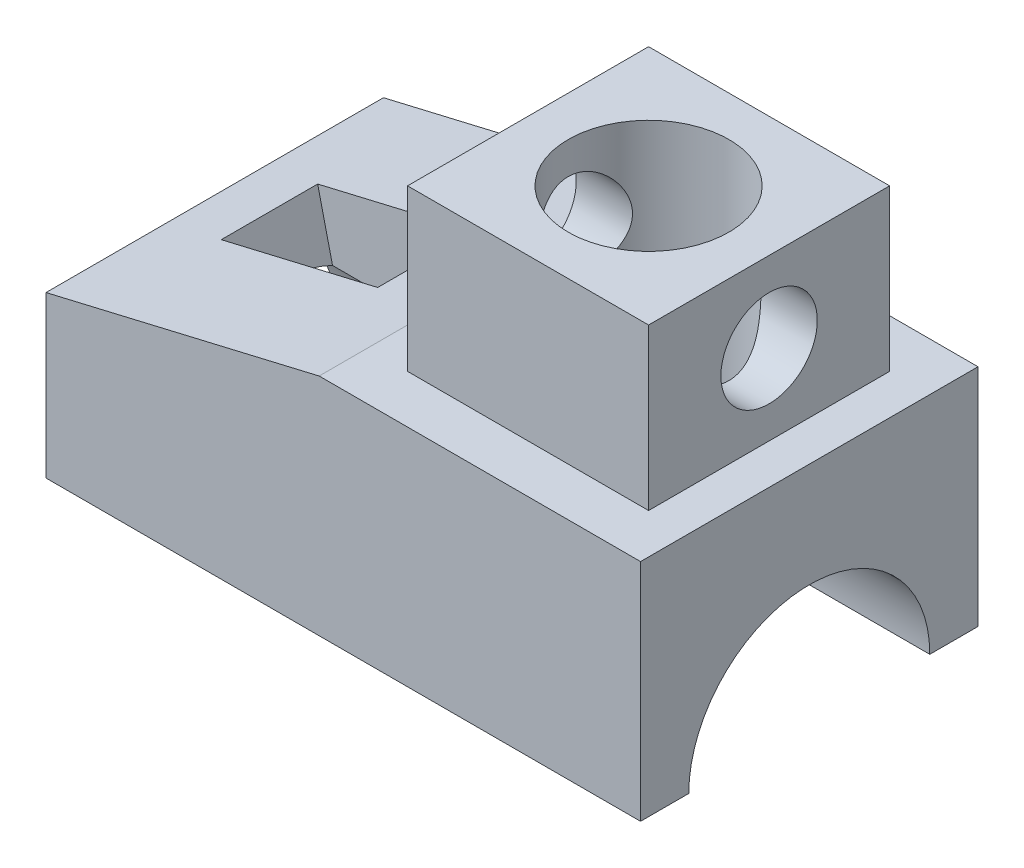
SolidWorks part; units mm, degrees
ref_plane "Front Plane" through (0, 0, 0) normal (0, 0, 1) x (1, 0, 0)
ref_plane "Top Plane" through (0, 0, 0) normal (0, 1, 0) x (1, 0, 0)
ref_plane "Right Plane" through (0, 0, 0) normal (1, 0, 0) x (0, 0, -1)
sketch "Sketch1" plane through (0, 0, 0) normal (0, 0, 1) x (1, 0, 0)
  line L0 (0, 0) -> (74, 0)
  line L1 (74, 0) -> (74, 28)
  line L2 (74, 28) -> (34, 28)
  line L3 (34, 28) -> (0, 20)
  line L4 (0, 20) -> (0, 0)
  dimension "D1" = 74
  dimension "D2" = 28
  dimension "D3" = 40
  dimension "D4" = 20
extrude "Boss-Extrude1" add sketch "Sketch1" against normal blind 42
sketch "Sketch2" plane through (0, 0, 0) normal (-1, 0, 0) x (0, 0, 1)
  line L0 (-42, 0) -> (0, 0) construction
  circle A0 centre (-21, 0) radius 15
  dimension "D1" = 30
extrude "Cut-Extrude1" cut sketch "Sketch2" against normal blind 74
sketch "Sketch3" plane through (-4.459, 18.9508, 0) normal (-0.229, 0.9734, 0) x (0.9734, 0.229, 0)
  line L0 (4.5808, 42) -> (4.5808, 0) construction
  line L1 (31.5808, 27) -> (11.5808, 27)
  line L2 (31.5808, 27) -> (31.5808, 15)
  line L3 (31.5808, 15) -> (11.5808, 15)
  line L4 (11.5808, 27) -> (11.5808, 15)
  point P0 (22.045, 21)
  point P7 (22.045, 21)
  dimension "D1" = 20
  dimension "D2" = 12
  dimension "D3" = 7
extrude "Cut-Extrude4" cut sketch "Sketch3" against normal blind 74
sketch "Sketch4" plane through (0, 28, 0) normal (0, 1, 0) x (1, 0, 0)
  line L0 (74, 0) -> (34, 0) construction
  line L2 (69, 36) -> (39, 36)
  line L3 (69, 36) -> (69, 6)
  line L4 (69, 6) -> (39, 6)
  line L5 (39, 36) -> (39, 6)
  point P4 (54, 21)
  dimension "D1" = 30
  dimension "D2" = 30
  dimension "D3" = 6
extrude "Boss-Extrude2" add sketch "Sketch4" along normal blind 20
sketch "Sketch5" plane through (39, 0, 0) normal (-1, 0, 0) x (0, 0, 1)
  line L0 (-36, 48) -> (-6, 48) construction
  circle A0 centre (-21, 38) radius 6
  dimension "D1" = 12
  dimension "D2" = 10
extrude "Cut-Extrude5" cut sketch "Sketch5" against normal blind 30
sketch "Sketch6" plane through (0, 48, 0) normal (0, 1, 0) x (1, 0, 0)
  circle A0 centre (54, 21) radius 10
  dimension "D1" = 20
extrude "Cut-Extrude6" cut sketch "Sketch6" against normal blind 40
